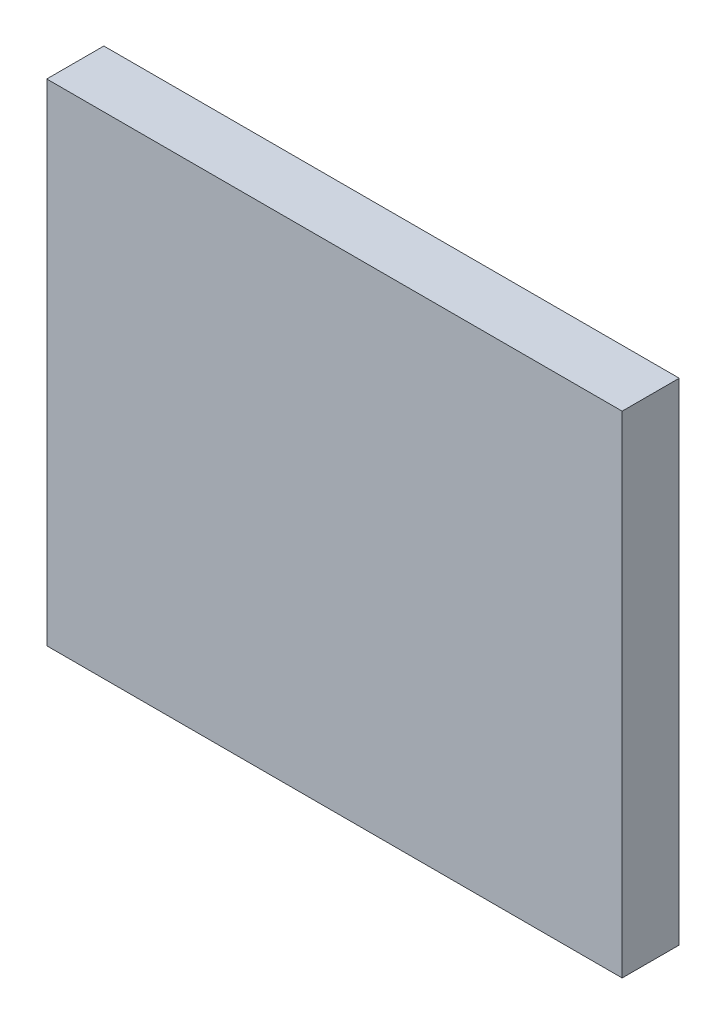
SolidWorks part; units mm, degrees
ref_plane "Front Plane" through (0, 0, 0) normal (0, 0, 1) x (1, 0, 0)
ref_plane "Top Plane" through (0, 0, 0) normal (0, 1, 0) x (1, 0, 0)
ref_plane "Right Plane" through (0, 0, 0) normal (1, 0, 0) x (0, 0, -1)
sketch "Sketch2" plane through (0, 0, 0) normal (0, 0, 1) x (1, 0, 0)
  line L1 (-12.6, -10.75) -> (12.6, -10.75)
  line L2 (-12.6, -10.75) -> (-12.6, 10.75)
  line L3 (-12.6, 10.75) -> (12.6, 10.75)
  line L4 (12.6, -10.75) -> (12.6, 10.75)
  line L5 (-12.6, -10.75) -> (12.6, 10.75) construction
  line L6 (-12.6, 10.75) -> (12.6, -10.75) construction
  point P0 (0, 0)
  dimension "D1" = 25.2
  dimension "D2" = 21.5
extrude "Boss-Extrude1" add sketch "Sketch2" along normal blind 2.5
